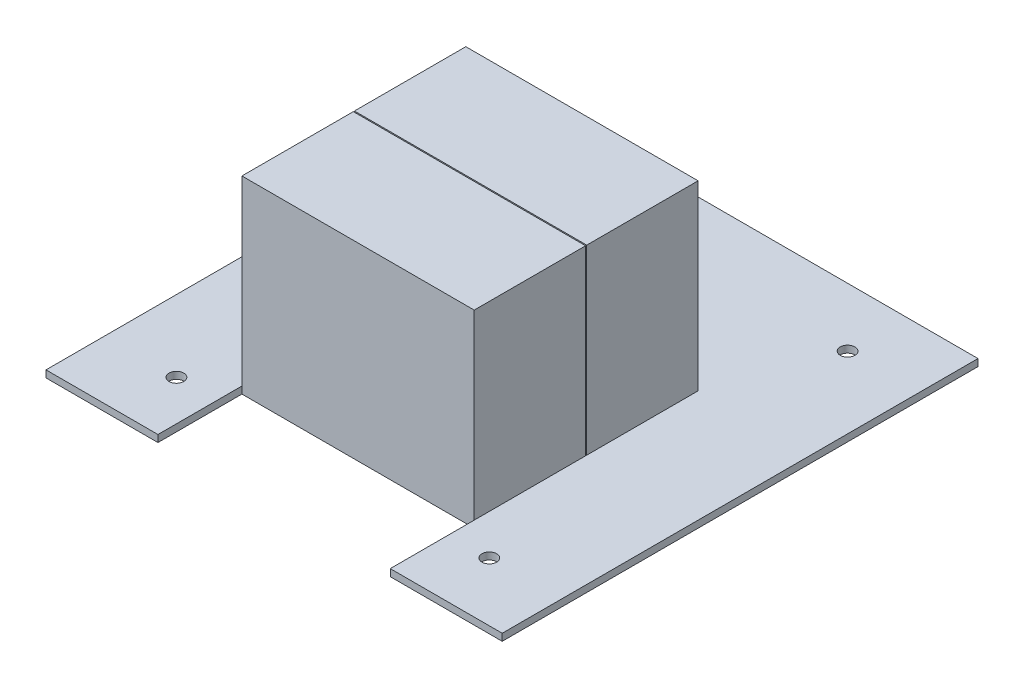
SolidWorks part; units mm, degrees
material "Plomo puro"
ref_plane "Alzado" through (0, 0, 0) normal (0, 0, 1) x (1, 0, 0)
ref_plane "Planta" through (0, 0, 0) normal (0, 1, 0) x (1, 0, 0)
ref_plane "Vista lateral" through (0, 0, 0) normal (1, 0, 0) x (0, 0, -1)
sketch "Croquis1" plane through (0, 0, 0) normal (0, 1, 0) x (1, 0, 0)
  line L0 (41.5, -85) -> (81.5, -85)
  line L1 (-81.5, 85) -> (81.5, 85)
  line L2 (-81.5, 85) -> (-81.5, -85)
  line L3 (-81.5, -85) -> (-41.5, -85)
  line L4 (81.5, 85) -> (81.5, -85)
  line L5 (-81.5, 85) -> (81.5, -85) construction
  line L6 (-81.5, -85) -> (81.5, 85) construction
  line L7 (41.5, -85) -> (41.5, -55)
  line L8 (41.5, -55) -> (-41.5, -55)
  line L9 (-41.5, -55) -> (-41.5, -85)
  point P0 (0, 0)
  dimension "D1" = 163
  dimension "D2" = 170
  dimension "D3" = 40
  dimension "D4" = 40
  dimension "D5" = 30
extrude "Saliente-Extruir1" add sketch "Croquis1" along normal blind 2.5
ref_plane "Plano1" through (0, 2.5, 0) normal (0, 1, 0) x (1, 0, 0)
sketch "Croquis2" plane through (0, 2.5, 0) normal (0, 1, 0) x (1, 0, 0)
  line L1 (-41.5, 25) -> (41.5, 25)
  line L2 (-41.5, 25) -> (-41.5, -55)
  line L3 (-41.5, -55) -> (41.5, -55)
  line L4 (41.5, 25) -> (41.5, -55)
  point P0 (0, 0)
  dimension "D1" = 80
extrude "Saliente-Extruir2" add sketch "Croquis2" along normal blind 65
ref_plane "Plano3" through (0, 70, 0) normal (0, 1, 0) x (1, 0, 0)
sketch "Croquis3" plane through (0, 70, 0) normal (0, 1, 0) x (1, 0, 0)
  line L0 (-41.5, -15) -> (-41.5, -14.8)
  line L1 (-41.5, 25) -> (-41.5, -55) construction
  line L2 (-41.5, -15) -> (41.5, -15) construction
  line L3 (41.5, -55) -> (41.5, 25) construction
  line L4 (-41.5, 25) -> (-41.5, -55) construction
  line L5 (-41.5, -14.8) -> (41.5, -14.8)
  line L6 (41.5, -14.8) -> (41.5, -15.2)
  line L7 (41.5, -55) -> (41.5, 25) construction
  line L8 (41.5, -15.2) -> (-41.5, -15.2)
  line L9 (-41.5, -15.2) -> (-41.5, -15)
  dimension "D1" = 0.2
  dimension "D2" = 0.2
extrude "Cortar-Extruir1" cut sketch "Croquis3" against normal through all
sketch "Croquis4" plane through (0, 0, 0) normal (0, 1, 0) x (1, 0, 0)
  line L0 (-81.5, 85) -> (-81.5, -85) construction
  line L1 (41.5, -85) -> (81.5, -85) construction
  line L2 (41.5, -64) -> (55.9, -64) construction
  line L4 (-81.5, -85) -> (-41.5, -85) construction
  line L5 (-55.9, -85) -> (-55.9, 85) construction
  line L6 (81.5, 85) -> (-81.5, 85) construction
  line L7 (-41.5, -85) -> (-41.5, -55) construction
  line L8 (-41.5, -64) -> (-55.9, -64) construction
  line L9 (41.5, -55) -> (41.5, -85) construction
  line L10 (55.9, -64) -> (55.9, 64) construction
  line L11 (55.9, 64) -> (-55.9, 64) construction
  circle A0 centre (-55.9, -64) radius 2.625
  circle A1 centre (55.9, -64) radius 2.625
  circle A2 centre (-55.9, 64) radius 2.625
  circle A3 centre (55.9, 64) radius 2.625
  dimension "D1" = 5.25
  dimension "D4" = 5.25
  dimension "D5" = 5.25
  dimension "D6" = 5.25
  dimension "D2" = 14.4
  dimension "D3" = 21
  dimension "D7" = 25.6
extrude "Cortar-Extruir2" cut sketch "Croquis4" along normal through all
